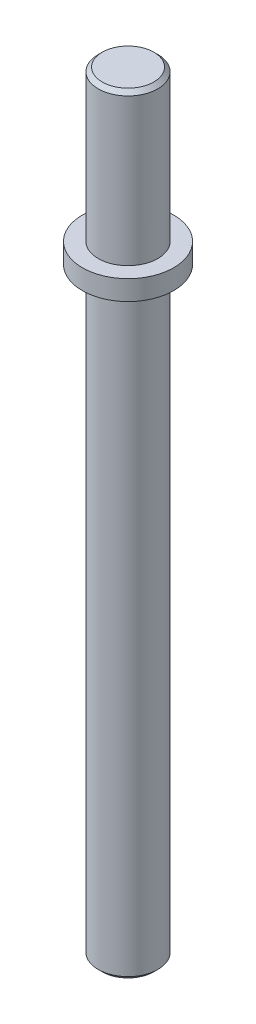
SolidWorks part; units mm, degrees
material "1060 Alloy"
ref_plane "Front Plane" through (0, 0, 0) normal (0, 0, 1) x (1, 0, 0)
ref_plane "Top Plane" through (0, 0, 0) normal (0, 1, 0) x (1, 0, 0)
ref_plane "Right Plane" through (0, 0, 0) normal (1, 0, 0) x (0, 0, -1)
sketch "Sketch1" plane through (0, 0, 0) normal (0, 0, 1) x (1, 0, 0)
  line L0 (1.905, 3.048) -> (1.905, -35.306)
  line L1 (0, 13.97) -> (1.905, 13.97)
  line L2 (0, 13.97) -> (0, -35.306)
  line L3 (0, -35.306) -> (1.905, -35.306)
  line L4 (1.905, 13.97) -> (1.905, 4.318)
  line L5 (1.905, 4.318) -> (2.921, 4.318)
  line L7 (1.905, 3.048) -> (2.921, 3.048)
  line L8 (2.921, 4.318) -> (2.921, 3.048)
  line L9 (0, 0) -> (0, 38.1556) construction
  dimension "D1" = 3.048
  dimension "D2" = 1.27
  dimension "D3" = 3.81
  dimension "D4" = 5.842
  dimension "D5" = 9.652
  dimension "D6" = 49.276
revolve "Revolve1" add sketch "Sketch1" angle 360 about L9
chamfer "Chamfer1" distance 0.254 angle 45 2 edges at (0, 13.97, -1.905) (0, -35.306, -1.905)
